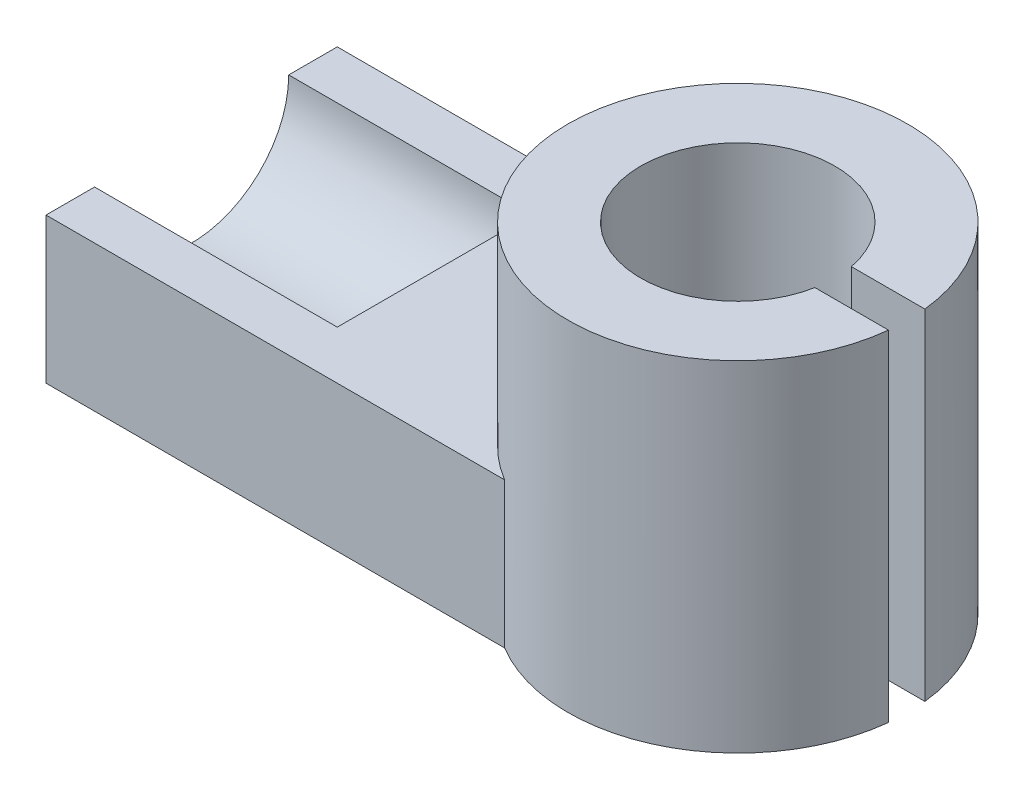
SolidWorks part; units mm, degrees
ref_plane "Front Plane" through (0, 0, 0) normal (0, 0, 1) x (1, 0, 0)
ref_plane "Top Plane" through (0, 0, 0) normal (0, 1, 0) x (1, 0, 0)
ref_plane "Right Plane" through (0, 0, 0) normal (1, 0, 0) x (0, 0, -1)
sketch "Sketch5" plane through (0, 0, 0) normal (0, 1, 0) x (1, 0, 0)
  line L1 (14.8406, -3) -> (28, -3)
  line L2 (15.0829, 3) -> (28, 3)
  circle A0 centre (0, 0) radius 28
  circle A1 centre (0, 0) radius 16
extrude "Boss-Extrude4" add sketch "Sketch5" along normal blind 56 contours A1 L2 A0 L1
sketch "Sketch6" plane through (0, 0, 0) normal (0, 1, 0) x (1, 0, 0)
  line L2 (0, -30.8) -> (0, 30.8) construction
  line L4 (-90, -24) -> (-90, 24)
  line L5 (-90, 24) -> (0, 24)
  line L7 (-90, -24) -> (0, -24)
  circle A0 centre (0, 0) radius 28
extrude "Boss-Extrude5" add sketch "Sketch6" along normal blind 24 contours A0 L5 L4 L7
sketch "Sketch7" plane through (-90, 0, 0) normal (-1, 0, 0) x (0, 0, 1)
  line L0 (24, 24) -> (-24, 24) construction
  circle A0 centre (0, 24) radius 16
extrude "Cut-Extrude1" cut sketch "Sketch7" against normal blind 40
sketch "Sketch8" plane through (0, 24, 0) normal (0, 1, 0) x (1, 0, 0)
  line L0 (-90, 16) -> (-50, 16)
  line L1 (15.7162, 3) -> (27.8388, 3) construction
  line L2 (15.7162, -3) -> (27.8388, -3) construction
  line L3 (-90, 24) -> (-14.4222, 24) construction
  line L4 (-90, -16) -> (-50, -16) construction
  line L5 (-90, -24) -> (-14.4222, -24) construction
  point P7 (21.7775, 3)
  point P8 (21.7775, -3)
  point P18 (-70, -16)
  point P19 (-52.2111, -24)
  dimension "D1" = 40
  dimension "D2" = 6
  dimension "D3" = 32
  dimension "D4" = 8
  dimension "D5" = 8
sketch "Sketch9" plane through (0, 56, 0) normal (0, 1, 0) x (1, 0, 0)
  line L0 (0, 28) -> (0, -28) construction
  line L1 (0, -30.8) -> (0, 30.8) construction
  line L2 (-28, 0) -> (29.3148, 0) construction
  line L3 (-30.8, 0) -> (30.8, 0) construction
  arc A0 (27.8388, 3) -> (27.8388, -3) centre (0, 0) ccw construction
  arc A1 (-14.4222, 24) -> (-14.4222, -24) centre (0, 0) ccw construction
sketch "Sketch10" plane through (0, 0, 0) normal (1, 0, 0) x (0, 0, -1)
  line L0 (0, 58.8411) -> (0, 0) construction
